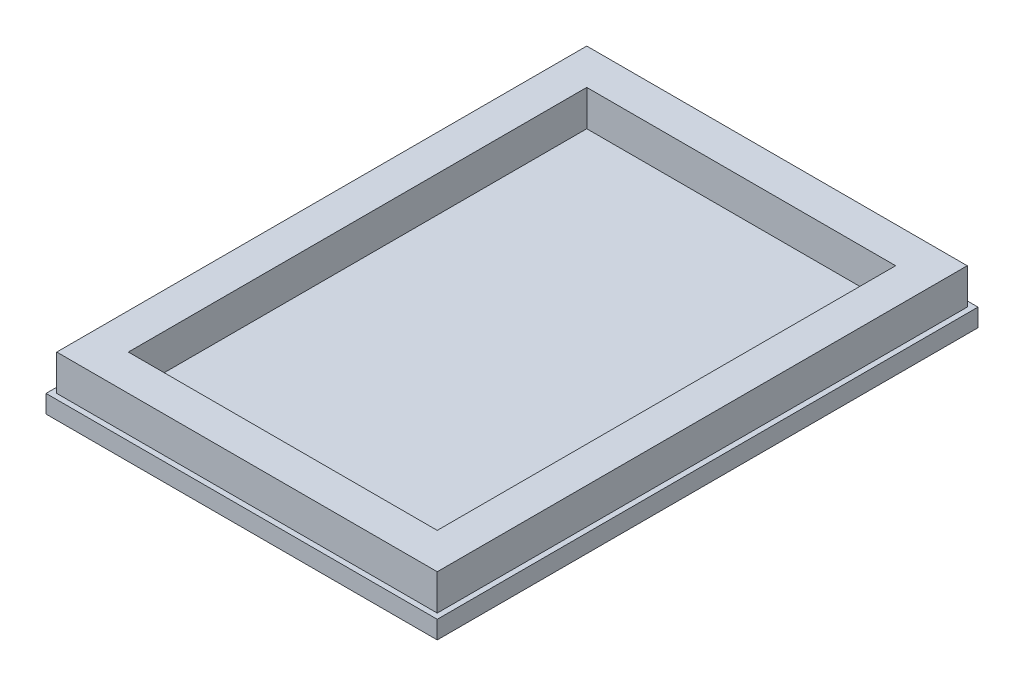
SolidWorks part; units mm, degrees
ref_plane "Front Plane" through (0, 0, 0) normal (0, 0, 1) x (1, 0, 0)
ref_plane "Top Plane" through (0, 0, 0) normal (0, 1, 0) x (1, 0, 0)
ref_plane "Right Plane" through (0, 0, 0) normal (1, 0, 0) x (0, 0, -1)
sketch "Sketch1" plane through (0, 0, 0) normal (0, 1, 0) x (1, 0, 0)
  line L1 (-10.925, 15.1) -> (10.925, 15.1)
  line L2 (-10.925, 15.1) -> (-10.925, -15.1)
  line L3 (-10.925, -15.1) -> (10.925, -15.1)
  line L4 (10.925, 15.1) -> (10.925, -15.1)
  line L5 (-10.925, 15.1) -> (10.925, -15.1) construction
  line L6 (-10.925, -15.1) -> (10.925, 15.1) construction
  point P0 (0, 0)
  dimension "D1" = 21.85
  dimension "D2" = 30.2
extrude "Boss-Extrude1" add sketch "Sketch1" along normal blind 1
sketch "Sketch2" plane through (0, 1, 0) normal (0, 1, 0) x (1, 0, 0)
  line L4 (8.625, -12.8) -> (8.625, 12.8)
  line L5 (8.625, 12.8) -> (-8.625, 12.8)
  line L6 (-8.625, 12.8) -> (-8.625, -12.8)
  line L7 (-8.625, -12.8) -> (8.625, -12.8)
  line L8 (10.625, -14.8) -> (10.625, 14.8)
  line L9 (10.625, 14.8) -> (-10.625, 14.8)
  line L10 (-10.625, 14.8) -> (-10.625, -14.8)
  line L11 (-10.625, -14.8) -> (10.625, -14.8)
  line L12 (10.625, -14.8) -> (10.625, 14.8)
  line L13 (10.625, 14.8) -> (-10.625, 14.8)
  line L14 (-10.625, 14.8) -> (-10.625, -14.8)
  line L15 (-10.625, -14.8) -> (10.625, -14.8)
  dimension "D1" = 0.3
  dimension "D2" = 2
extrude "Boss-Extrude2" add sketch "Sketch2" along normal blind 2
